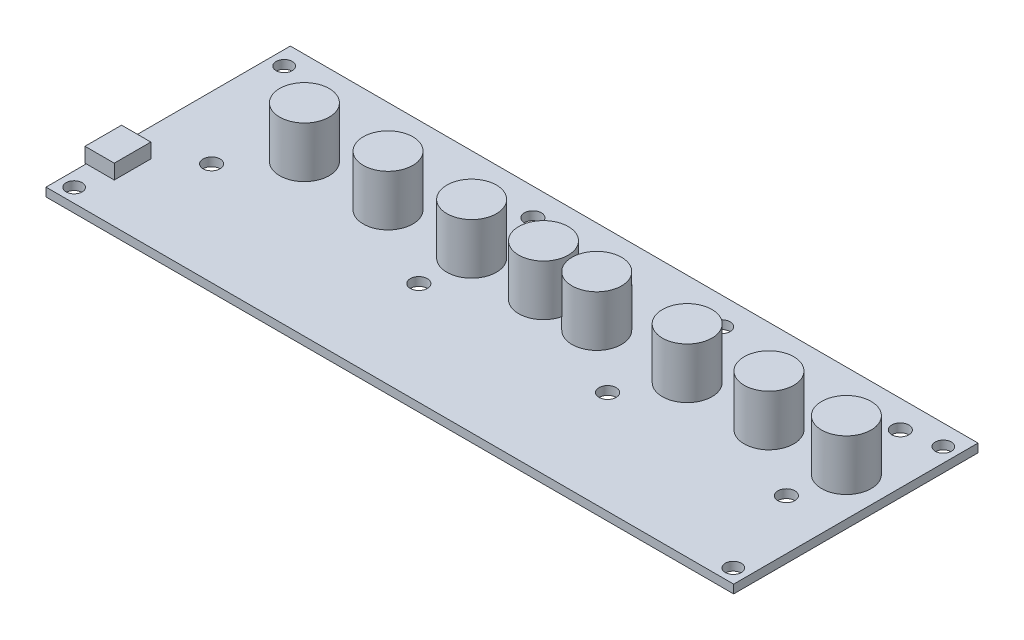
SolidWorks part; units mm, degrees
ref_plane "Front Plane" through (0, 0, 0) normal (0, 0, 1) x (1, 0, 0)
ref_plane "Top Plane" through (0, 0, 0) normal (0, 1, 0) x (1, 0, 0)
ref_plane "Right Plane" through (0, 0, 0) normal (1, 0, 0) x (0, 0, -1)
sketch "Sketch1" plane through (0, 0, 0) normal (0, 1, 0) x (1, 0, 0)
  line L1 (-70.5, -25.05) -> (70.5, -25.05)
  line L2 (-70.5, -25.05) -> (-70.5, 25.05)
  line L3 (-70.5, 25.05) -> (70.5, 25.05)
  line L4 (70.5, -25.05) -> (70.5, 25.05)
  line L5 (-70.5, -25.05) -> (70.5, 25.05) construction
  line L6 (-70.5, 25.05) -> (70.5, -25.05) construction
  point P0 (0, 0)
  dimension "D1" = 141
  dimension "D2" = 50.1
extrude "Boss-Extrude1" add sketch "Sketch1" along normal mid plane 1.75
sketch "Sketch3" plane through (0, 0, 0) normal (0, 1, 0) x (1, 0, 0)
  line L0 (69.23, 20.859) -> (70.5, 20.859) construction
  line L1 (70.5, -25.05) -> (70.5, 25.05) construction
  line L2 (67.579, 22.51) -> (67.579, 25.05) construction
  line L3 (70.5, 25.05) -> (-70.5, 25.05) construction
  line L4 (67.579, -22.199) -> (67.579, -25.05) construction
  line L5 (-70.5, -25.05) -> (70.5, -25.05) construction
  circle A0 centre (67.579, 20.859) radius 1.651
  circle A1 centre (67.579, -22.199) radius 1.651
  point P12 (67.579, -23.85)
  dimension "D3" = 3.302
  dimension "D1" = 1.27
  dimension "D2" = 2.54
  dimension "D4" = 1.2
extrude "Cut-Extrude1" cut sketch "Sketch3" against normal through all both and the other way through all
sketch "Sketch4" plane through (0, 0, 0) normal (0, 1, 0) x (1, 0, 0)
  line L0 (-57.65, 19.425) -> (-15.15, 19.425) construction
  line L1 (-70.5, 25.05) -> (-70.5, -25.05) construction
  line L2 (70.5, 25.05) -> (-70.5, 25.05) construction
  line L3 (-15.15, 19.425) -> (-15.15, -3.95) construction
  line L4 (-15.15, -3.95) -> (23.55, -3.95) construction
  line L5 (23.55, -3.95) -> (23.55, 19.425) construction
  line L6 (23.55, 19.425) -> (60.2, 19.425) construction
  line L7 (60.2, 19.425) -> (60.2, -3.95) construction
  line L8 (-57.65, -3.95) -> (-57.65, 19.425) construction
  circle A0 centre (-57.65, 19.425) radius 1.75
  circle A1 centre (-15.15, 19.425) radius 1.75
  circle A2 centre (23.55, 19.425) radius 1.75
  circle A3 centre (60.2, 19.425) radius 1.75
  circle A4 centre (-15.15, -3.95) radius 1.75
  circle A5 centre (23.55, -3.95) radius 1.75
  circle A6 centre (60.2, -3.95) radius 1.75
  circle A7 centre (-57.65, -3.95) radius 1.75
  point P2 (-59.4, 19.425)
  point P5 (-57.65, 21.175)
  dimension "D3" = 3.5
  dimension "D1" = 11.1
  dimension "D2" = 3.875
  dimension "D4" = 23.375
  dimension "D5" = 42.5
  dimension "D6" = 38.7
  dimension "D7" = 36.65
extrude "Cut-Extrude2" cut sketch "Sketch4" against normal through all both and the other way through all
mirror "Mirror1" about plane through (0, 0, 0) normal (1, 0, 0) of "Cut-Extrude1"
sketch "Sketch2" plane through (0, 0.875, 0) normal (0, 1, 0) x (1, 0, 0)
  line L0 (-48.5625, 6) -> (-31.4175, 6) construction
  line L1 (-31.4175, 6) -> (-14.2725, 6) construction
  line L2 (-14.2725, 6) -> (0.4595, 6) construction
  line L3 (0.4595, 6) -> (11.3815, 6) construction
  line L4 (11.3815, 6) -> (29.9235, 6) construction
  line L5 (29.9235, 6) -> (46.6875, 6) construction
  line L6 (46.6875, 6) -> (62.5625, 6) construction
  line L7 (70.5, 25.05) -> (-70.5, 25.05) construction
  line L8 (70.5, -25.05) -> (70.5, 25.05) construction
  circle A0 centre (-48.5625, 6) radius 5.08
  circle A1 centre (-31.4175, 6) radius 5.08
  circle A2 centre (-14.2725, 6) radius 5.08
  circle A3 centre (0.4595, 6) radius 5.08
  circle A4 centre (11.3815, 6) radius 5.08
  circle A5 centre (29.9235, 6) radius 5.08
  circle A6 centre (46.6875, 6) radius 5.08
  circle A7 centre (62.5625, 6) radius 5.08
  dimension "D1" = 10.16
  dimension "D2" = 15.875
  dimension "D3" = 16.764
  dimension "D4" = 18.542
  dimension "D5" = 10.922
  dimension "D6" = 14.732
  dimension "D7" = 17.145
  dimension "D8" = 111.125
  dimension "D9" = 19.05
  dimension "D10" = 7.9375
extrude "Boss-Extrude2" add sketch "Sketch2" along normal blind 10.414
sketch "Sketch5" plane through (-70.5, 0, 0) normal (-1, 0, 0) x (0, 0, 1)
  line L0 (-25.05, 0.875) -> (25.05, 0.875) construction
  line L1 (9.3, 0.875) -> (16.8, 0.875)
  line L2 (9.3, 0.875) -> (9.3, 3.875)
  line L3 (9.3, 3.875) -> (16.8, 3.875)
  line L4 (16.8, 0.875) -> (16.8, 3.875)
  line L5 (25.05, 0.875) -> (25.05, -0.875) construction
  point P6 (18.977, 3.875)
  dimension "D1" = 7.5
  dimension "D2" = 3
  dimension "D3" = 8.25
extrude "Boss-Extrude3" add sketch "Sketch5" against normal blind 6 from offset 0.254
